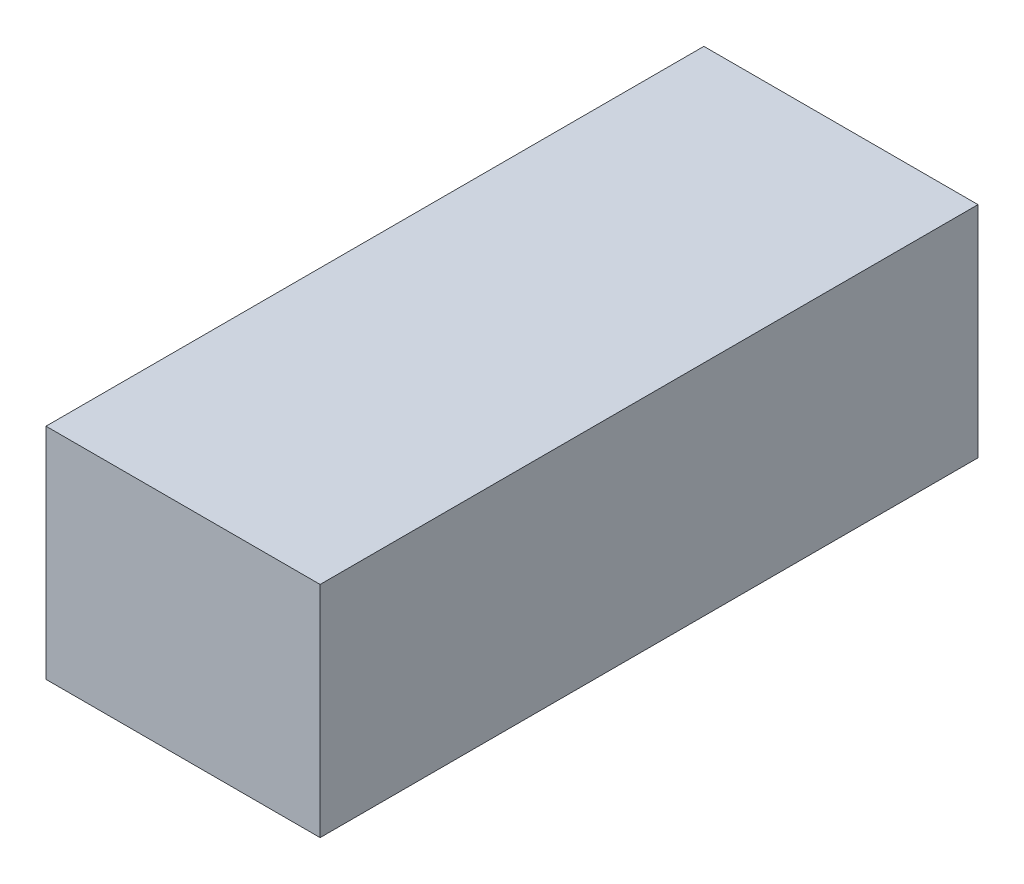
SolidWorks part; units mm, degrees
ref_plane "Alzado" through (0, 0, 0) normal (0, 0, 1) x (1, 0, 0)
ref_plane "Planta" through (0, 0, 0) normal (0, 1, 0) x (1, 0, 0)
ref_plane "Vista lateral" through (0, 0, 0) normal (1, 0, 0) x (0, 0, -1)
sketch "Croquis1" plane through (0, 0, 0) normal (0, 0, 1) x (1, 0, 0)
  line L1 (-12.5, 10) -> (12.5, 10)
  line L2 (-12.5, 10) -> (-12.5, -10)
  line L3 (-12.5, -10) -> (12.5, -10)
  line L4 (12.5, 10) -> (12.5, -10)
  line L5 (-12.5, 10) -> (12.5, -10) construction
  line L6 (-12.5, -10) -> (12.5, 10) construction
  point P0 (0, 0)
  dimension "D1" = 20
  dimension "D2" = 25
extrude "Saliente-Extruir1" add sketch "Croquis1" along normal mid plane 60
